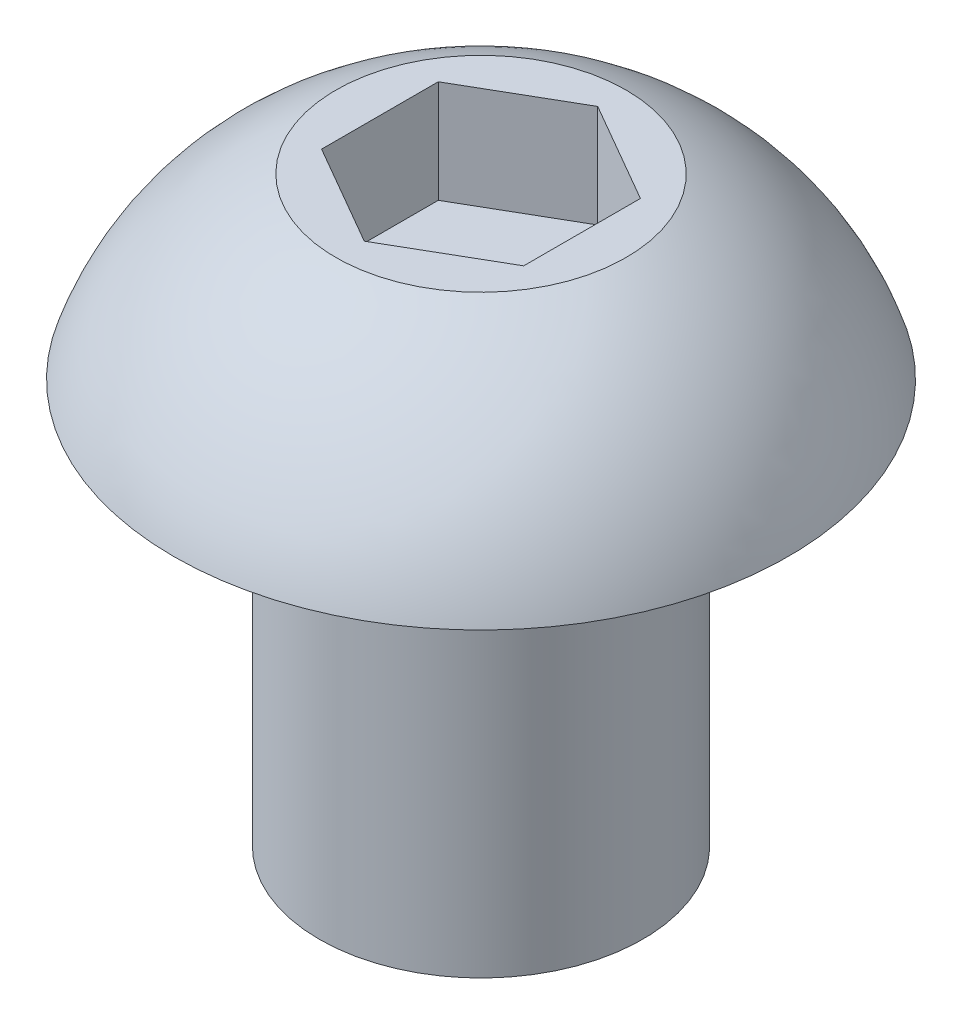
SolidWorks part; units mm, degrees
material "AISI Type 316L stainless steel"
ref_plane "Front Plane" through (0, 0, 0) normal (0, 0, 1) x (1, 0, 0)
ref_plane "Top Plane" through (0, 0, 0) normal (0, 1, 0) x (1, 0, 0)
ref_plane "Right Plane" through (0, 0, 0) normal (1, 0, 0) x (0, 0, -1)
sketch "Sketch1" plane through (0, 0, 0) normal (0, 0, 1) x (1, 0, 0)
  line L0 (-2, 0) -> (-3.8, 0)
  line L1 (-2, 0) -> (-2, -5)
  line L2 (0, -5) -> (0, 2.2)
  line L3 (0, 2.2) -> (-1.7948, 2.2)
  line L4 (-2, -5) -> (0, -5)
  arc A0 (-3.8, 0) -> (-1.7948, 2.2) centre (-0.4063, -1.0794) cw
  dimension "D1" = 5
  dimension "D2" = 2.2
  dimension "D3" = 3.8
  dimension "D4" = 2
  dimension "D5" = 1.7948
revolve "Revolve1" add sketch "Sketch1" angle 360 about L2
sketch "Sketch2" plane through (0, 2.2, 0) normal (0, 1, 0) x (1, 0, 0)
  line L0 (0, 0) -> (0, 1.4434) construction
  line L1 (-1.25, 0.7217) -> (-1.25, -0.7217)
  line L2 (-1.25, -0.7217) -> (0, -1.4434)
  line L3 (0, -1.4434) -> (1.25, -0.7217)
  line L4 (1.25, -0.7217) -> (1.25, 0.7217)
  line L5 (1.25, 0.7217) -> (0, 1.4434)
  line L6 (0, 1.4434) -> (-1.25, 0.7217)
  circle A0 centre (0, 0) radius 1.25 construction
  dimension "D1" = 2.5
extrude "Cut-Extrude1" cut sketch "Sketch2" against normal blind 1.27
